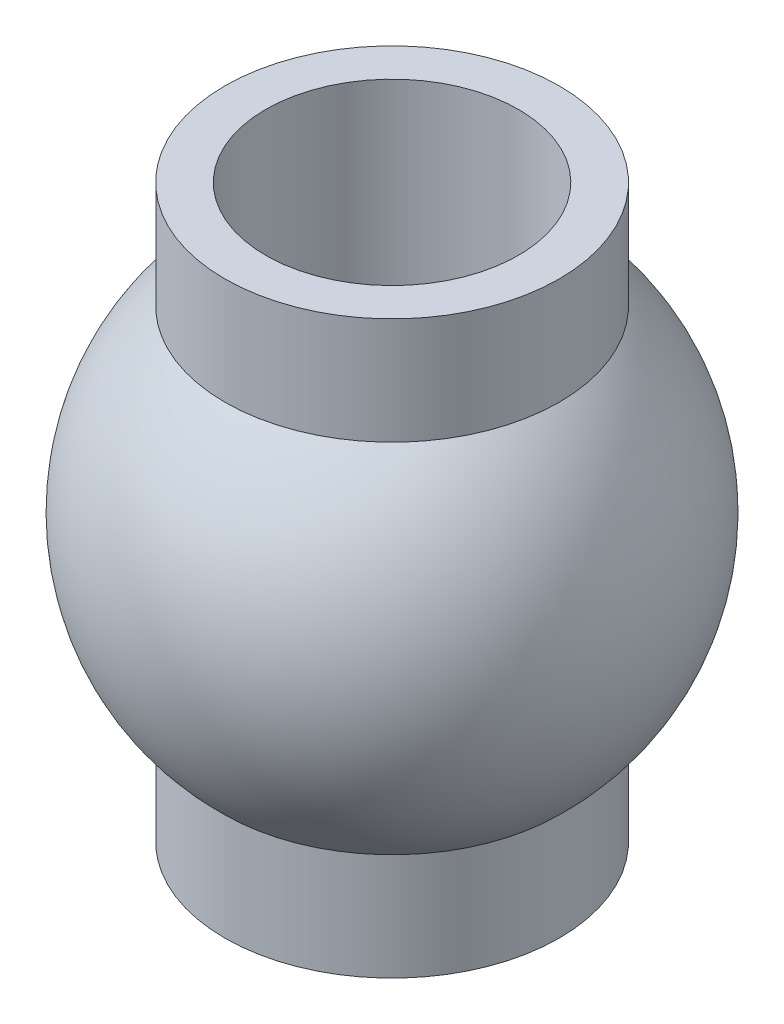
SolidWorks part; units mm, degrees
material "Brass"
ref_plane "Front Plane" through (0, 0, 0) normal (0, 0, 1) x (1, 0, 0)
ref_plane "Top Plane" through (0, 0, 0) normal (0, 1, 0) x (1, 0, 0)
ref_plane "Right Plane" through (0, 0, 0) normal (1, 0, 0) x (0, 0, -1)
sketch "Sketch2" plane through (0, 0, 0) normal (0, 0, 1) x (1, 0, 0)
  line L0 (1.55, 3.5) -> (1.55, -3.5)
  line L3 (1.55, 3.5) -> (2.05, 3.5)
  line L4 (2.05, 2.1903) -> (2.05, 3.5)
  line L5 (0, 3.5) -> (0, -3.5) construction
  line L7 (1.55, -3.5) -> (2.05, -3.5)
  line L8 (2.05, -3.5) -> (2.05, -2.1903)
  arc A1 (2.05, -2.1903) -> (2.05, 2.1903) centre (0, 0) ccw
  point P9 (1.55, 0)
  dimension "D1" = 3
  dimension "D2" = 0.5
  dimension "D3" = 1.55
  dimension "D4" = 0.5
  dimension "D5" = 7
revolve "Revolve1" add sketch "Sketch2" angle 360 about L5
